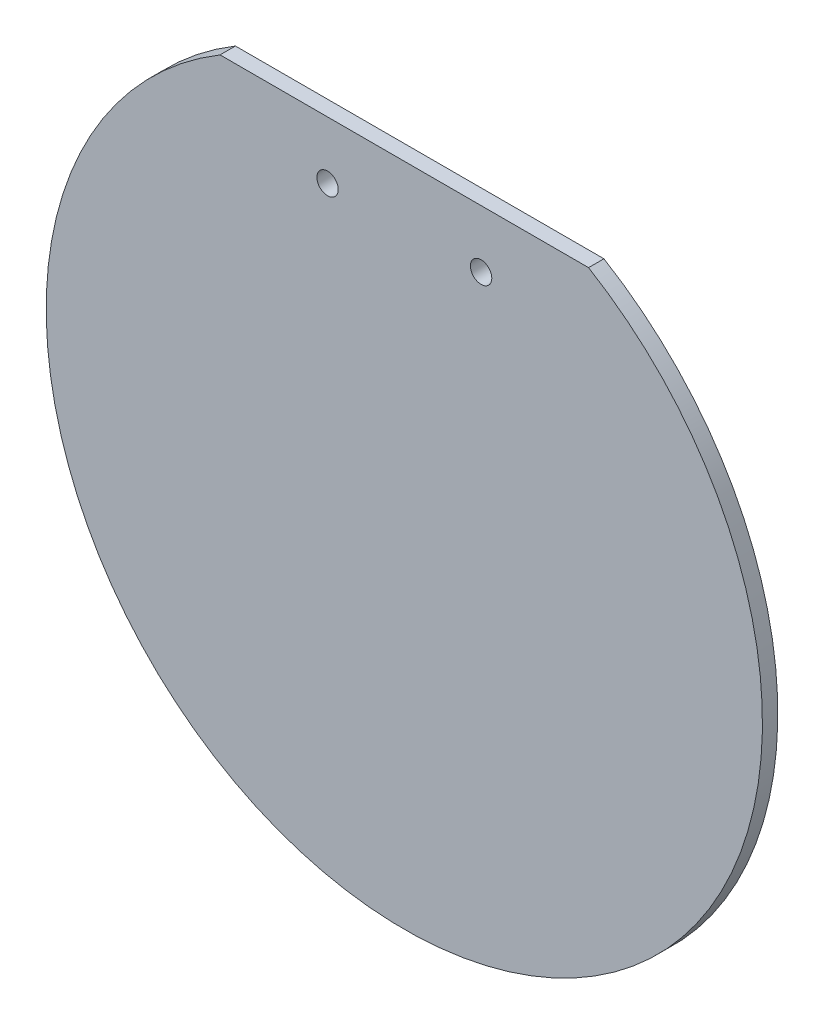
SolidWorks part; units mm, degrees
ref_plane "Front Plane" through (0, 0, 0) normal (0, 0, 1) x (1, 0, 0)
ref_plane "Top Plane" through (0, 0, 0) normal (0, 1, 0) x (1, 0, 0)
ref_plane "Right Plane" through (0, 0, 0) normal (1, 0, 0) x (0, 0, -1)
sketch "Sketch1" plane through (0, 0, 0) normal (0, 0, 1) x (1, 0, 0)
  line L0 (-19.05, 31.75) -> (19.05, 31.75) construction
  line L1 (0, 31.75) -> (0, 0) construction
  line L2 (-19.05, 31.75) -> (19.05, 31.75)
  circle A0 centre (0, 0) radius 37.0265 construction
  arc A1 (-19.05, 31.75) -> (19.05, 31.75) centre (0, 0) ccw
  dimension "D1" = 38.1
  dimension "D2" = 31.75
extrude "Boss-Extrude1" add sketch "Sketch1" along normal blind 1.5875
sketch "Sketch3" plane through (0, 0, 1.5875) normal (0, 0, 1) x (1, 0, 0)
  circle A3 centre (7.9375, 25.7962) radius 1.1049
  circle A5 centre (-7.9375, 25.7962) radius 1.1049
  dimension "D1" = 2.2098
extrude "Cut-Extrude1" cut sketch "Sketch3" against normal through all
